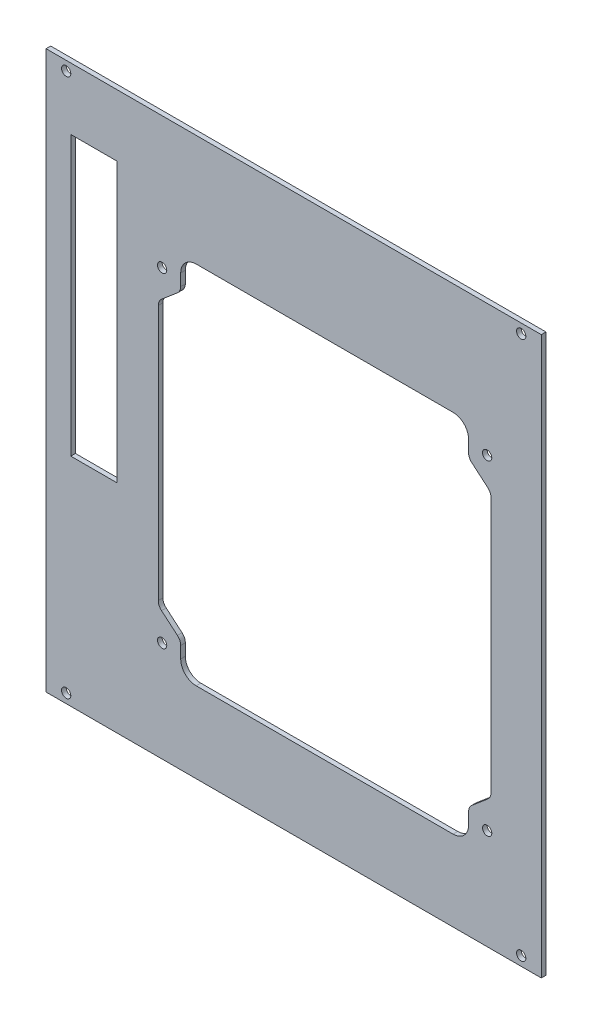
SolidWorks part; units mm, degrees
material "1060 合金"
ref_plane "前视基准面" through (0, 0, 0) normal (0, 0, 1) x (1, 0, 0)
ref_plane "上视基准面" through (0, 0, 0) normal (0, 1, 0) x (1, 0, 0)
ref_plane "右视基准面" through (0, 0, 0) normal (1, 0, 0) x (0, 0, -1)
sketch "草图1" plane through (0, 0, 0) normal (0, 0, 1) x (1, 0, 0)
  line L0 (-1490.0693, 900) -> (-1490.0693, -900)
  line L1 (-1490.0693, -900) -> (109.9307, -900)
  line L2 (109.9307, -900) -> (109.9307, 900)
  line L3 (109.9307, 900) -> (-1490.0693, 900)
  line L4 (-175.0693, -640) -> (-1005.0693, -640)
  line L5 (-1055.0693, -590) -> (-1055.0693, -552.1017)
  line L6 (-1065.6554, -529.2303) -> (-1116.9832, -485.6618)
  line L7 (-1127.5693, -462.7904) -> (-1127.5693, 362.7904)
  line L8 (-1116.9832, 385.6618) -> (-1065.6554, 429.2303)
  line L9 (-1055.0693, 452.1017) -> (-1055.0693, 490)
  line L10 (-1005.0693, 540) -> (-175.0693, 540)
  line L11 (-125.0693, 490) -> (-125.0693, 452.1017)
  line L12 (-114.4832, 429.2303) -> (-63.1554, 385.6618)
  line L13 (-52.5693, 362.7904) -> (-52.5693, -462.7904)
  line L14 (-63.1554, -485.6618) -> (-114.4832, -529.2303)
  line L15 (-125.0693, -552.1017) -> (-125.0693, -590)
  line L17 (-1410.0693, 700) -> (-1260.0693, 700)
  line L18 (-1410.0693, 700) -> (-1410.0693, -200)
  line L19 (-1410.0693, -200) -> (-1260.0693, -200)
  line L20 (-1260.0693, 700) -> (-1260.0693, -200)
  arc A0 (-1055.0693, -590) -> (-1005.0693, -640) centre (-1005.0693, -590) ccw
  arc A1 (-1055.0693, -552.1017) -> (-1065.6554, -529.2303) centre (-1085.0693, -552.1017) ccw
  arc A2 (-1127.5693, -462.7904) -> (-1116.9832, -485.6618) centre (-1097.5693, -462.7904) ccw
  arc A3 (-1116.9832, 385.6618) -> (-1127.5693, 362.7904) centre (-1097.5693, 362.7904) ccw
  arc A4 (-1065.6554, 429.2303) -> (-1055.0693, 452.1017) centre (-1085.0693, 452.1017) ccw
  arc A5 (-1005.0693, 540) -> (-1055.0693, 490) centre (-1005.0693, 490) ccw
  arc A6 (-125.0693, 490) -> (-175.0693, 540) centre (-175.0693, 490) ccw
  arc A7 (-125.0693, 452.1017) -> (-114.4832, 429.2303) centre (-95.0693, 452.1017) ccw
  arc A8 (-52.5693, 362.7904) -> (-63.1554, 385.6618) centre (-82.5693, 362.7904) ccw
  arc A9 (-63.1554, -485.6618) -> (-52.5693, -462.7904) centre (-82.5693, -462.7904) ccw
  arc A10 (-114.4832, -529.2303) -> (-125.0693, -552.1017) centre (-95.0693, -552.1017) ccw
  arc A11 (-175.0693, -640) -> (-125.0693, -590) centre (-175.0693, -590) ccw
  circle A12 centre (-1425.0693, 870) radius 15
  circle A13 centre (-1425.0693, -870) radius 15
  circle A14 centre (44.9307, -870) radius 15
  circle A15 centre (44.9307, 870) radius 15
  circle A16 centre (-65.0693, -575) radius 15
  circle A17 centre (-65.0693, 475) radius 15
  circle A18 centre (-1115.0693, 475) radius 15
  circle A19 centre (-1115.0693, -575) radius 15
  dimension "D7" = 200
  dimension "D8" = 900
  dimension "D9" = 80
  dimension "D11" = 150
  dimension "D27" = 30
  dimension "D32" = 65
  dimension "D33" = 30
  dimension "D49" = 1050
  dimension "D50" = 375
  dimension "D53" = 425
  dimension "D54" = 425
  dimension "D56" = 325
  dimension "D58" = 375
  dimension "D103" = 30
  dimension "D105" = 50
  dimension "D21" = 1600
  dimension "D22" = 1800
  dimension "D28" = 65
  dimension "D55" = 325
  dimension "D57" = 1050
  dimension "D60" = 1050
extrude "凸台-拉伸1" add sketch "草图1" along normal blind 3
scale "缩放比例1" bodies to scale 101 104 102 103 108 scale about centroid uniform scaling no x scale factor 0.1 y scale factor 0.1 z scale factor 0.5
